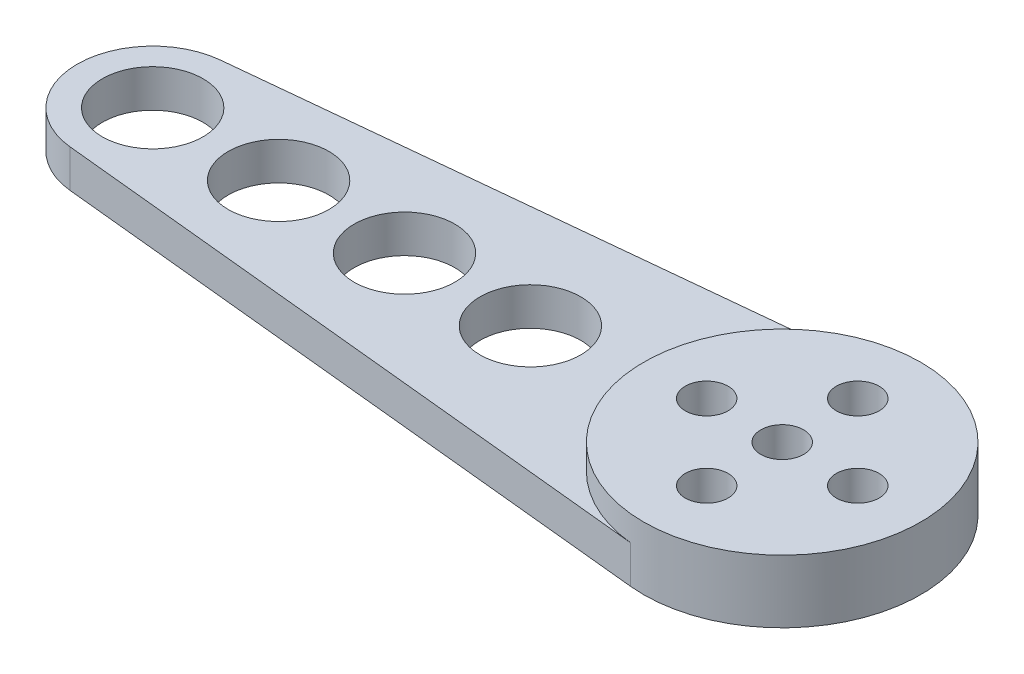
SolidWorks part; units mm, degrees
material "ABS"
ref_plane "Plan de face" through (0, 0, 0) normal (0, 0, 1) x (1, 0, 0)
ref_plane "Plan de dessus" through (0, 0, 0) normal (0, 1, 0) x (1, 0, 0)
ref_plane "Plan de droite" through (0, 0, 0) normal (1, 0, 0) x (0, 0, -1)
sketch "Esquisse1" plane through (0, 0, 0) normal (0, 1, 0) x (1, 0, 0)
  line L0 (0, 0) -> (-50, 0) construction
  line L1 (-50.6, 5.9699) -> (-1.1, 10.9449)
  line L2 (-50.6, -5.9699) -> (-1.1, -10.9449)
  arc A0 (-1.1, -10.9449) -> (-1.1, 10.9449) centre (0, 0) ccw
  arc A1 (-50.6, 5.9699) -> (-50.6, -5.9699) centre (-50, 0) ccw
  circle A2 centre (-50, 0) radius 4
  circle A3 centre (-40, 0) radius 4
  circle A4 centre (-30, 0) radius 4
  circle A5 centre (-20, 0) radius 4
  point P15 (-23.9498, 0)
  point P16 (-15.2104, 0)
  point P17 (-33.5214, 0)
  dimension "D1" = 22
  dimension "D2" = 8
  dimension "D3" = 6
  dimension "D4" = 10
  dimension "D5" = 10
  dimension "D6" = 10
  dimension "D7" = 50
extrude "Boss.-Extru.1" add sketch "Esquisse1" along normal blind 3
sketch "Esquisse2" plane through (0, 3, 0) normal (0, 1, 0) x (1, 0, 0)
  circle A0 centre (0, 0) radius 11
extrude "Boss.-Extru.2" add sketch "Esquisse2" along normal blind 2
sketch "Esquisse4" plane through (0, 5, 0) normal (0, 1, 0) x (1, 0, 0)
  circle A0 centre (0, 0) radius 1.7
  circle A1 centre (0, 0) radius 6 construction
  circle A2 centre (0, 6) radius 1.7
  circle A3 centre (6, 0) radius 1.7
  circle A4 centre (0, -6) radius 1.7
  circle A5 centre (-6, 0) radius 1.7
  point P15 (0, 0)
  dimension "D1" = 3.4
  dimension "D2" = 12
  dimension "D3" = 3.4
  dimension "D4" = 4
extrude "Enlèv. mat.-Extru.1" cut sketch "Esquisse4" against normal through all
sketch "Esquisse5" plane through (0, 0, 0) normal (0, -1, 0) x (1, 0, 0)
  line L1 (-2.75, -2.75) -> (2.75, -2.75)
  line L2 (-2.75, -2.75) -> (-2.75, 2.75)
  line L3 (-2.75, 2.75) -> (2.75, 2.75)
  line L4 (2.75, -2.75) -> (2.75, 2.75)
  line L5 (-2.75, -2.75) -> (2.75, 2.75) construction
  line L6 (-2.75, 2.75) -> (2.75, -2.75) construction
  point P0 (0, 0)
  dimension "D1" = 5.5
extrude "Enlèv. mat.-Extru.2" cut sketch "Esquisse5" against normal blind 1.5
